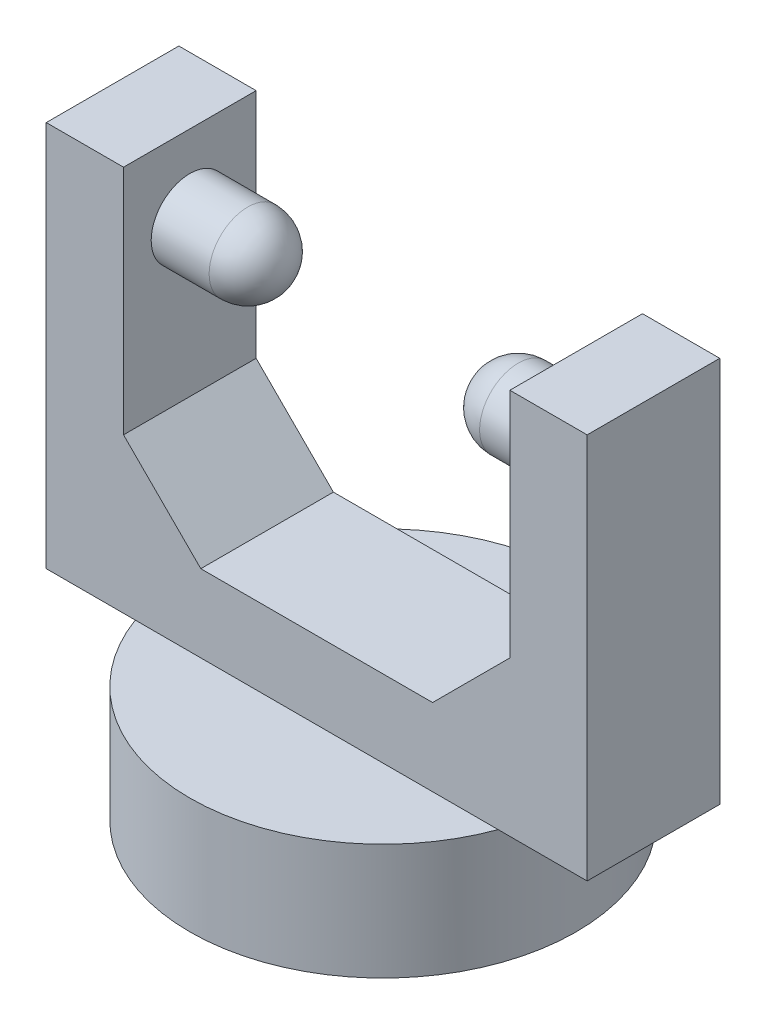
SolidWorks part; units mm, degrees
ref_plane "Front Plane" through (0, 0, 0) normal (0, 0, 1) x (1, 0, 0)
ref_plane "Top Plane" through (0, 0, 0) normal (0, 1, 0) x (1, 0, 0)
ref_plane "Right Plane" through (0, 0, 0) normal (1, 0, 0) x (0, 0, -1)
sketch "Sketch1" plane through (0, 0, 0) normal (0, 1, 0) x (1, 0, 0)
  circle A0 centre (0, 0) radius 12.5
  dimension "D1" = 25
extrude "Boss-Extrude1" add sketch "Sketch1" along normal blind 7.5
sketch "Sketch2" plane through (0, 7.5, 0) normal (0, 1, 0) x (1, 0, 0)
  line L1 (-17.5, 4.2904) -> (17.5, 4.2904)
  line L2 (-17.5, 4.2904) -> (-17.5, -4.2904)
  line L3 (-17.5, -4.2904) -> (17.5, -4.2904)
  line L4 (17.5, 4.2904) -> (17.5, -4.2904)
  point P4 (17.5, 0)
  point P6 (0, 4.2904)
  dimension "D1" = 35
  dimension "D3" = 8.5808
extrude "Boss-Extrude2" add sketch "Sketch2" along normal blind 25
sketch "Sketch3" plane through (0, 32.5, 0) normal (0, 1, 0) x (1, 0, 0)
  line L0 (17.5, 4.2904) -> (-17.5, 4.2904) construction
  line L1 (-12.5, 4.2904) -> (12.5, 4.2904)
  line L2 (-12.5, 4.2904) -> (-12.5, -4.2904)
  line L3 (-12.5, -4.2904) -> (12.5, -4.2904)
  line L4 (12.5, 4.2904) -> (12.5, -4.2904)
  line L5 (-17.5, -4.2904) -> (17.5, -4.2904) construction
  line L6 (17.5, -4.2904) -> (17.5, 4.2904) construction
  line L7 (-17.5, 4.2904) -> (-17.5, -4.2904) construction
  dimension "D1" = 5
  dimension "D2" = 5
extrude "Cut-Extrude1" cut sketch "Sketch3" against normal blind 20
sketch "Sketch4" plane through (-12.5, 0, 0) normal (1, 0, 0) x (0, 0, -1)
  line L0 (4.2904, 12.5) -> (-4.2904, 12.5) construction
  line L1 (4.2904, 32.5) -> (-4.2904, 32.5) construction
  circle A0 centre (0, 27.5) radius 2.5
  point P8 (0, 32.5)
  dimension "D1" = 5
  dimension "D2" = 15
extrude "Boss-Extrude3" add sketch "Sketch4" along normal blind 6.25
sketch "Sketch5" plane through (12.5, 0, 0) normal (-1, 0, 0) x (0, 0, 1)
  circle A0 centre (0, 27.5) radius 2.5
  circle A1 centre (0, 27.5) radius 2.5 construction
  dimension "D1" = 5
extrude "Boss-Extrude4" add sketch "Sketch5" along normal blind 6.25
chamfer "Chamfer1" distance 5 angle 45 1 edges at (-12.5, 12.5, 0)
chamfer "Chamfer2" distance 5 angle 45 1 edges at (12.5, 12.5, 0)
fillet "Fillet1" radius 2.5 1 edges at (-6.25, 27.5, -2.5)
fillet "Fillet2" radius 2.5 1 edges at (6.25, 27.5, 2.5)
